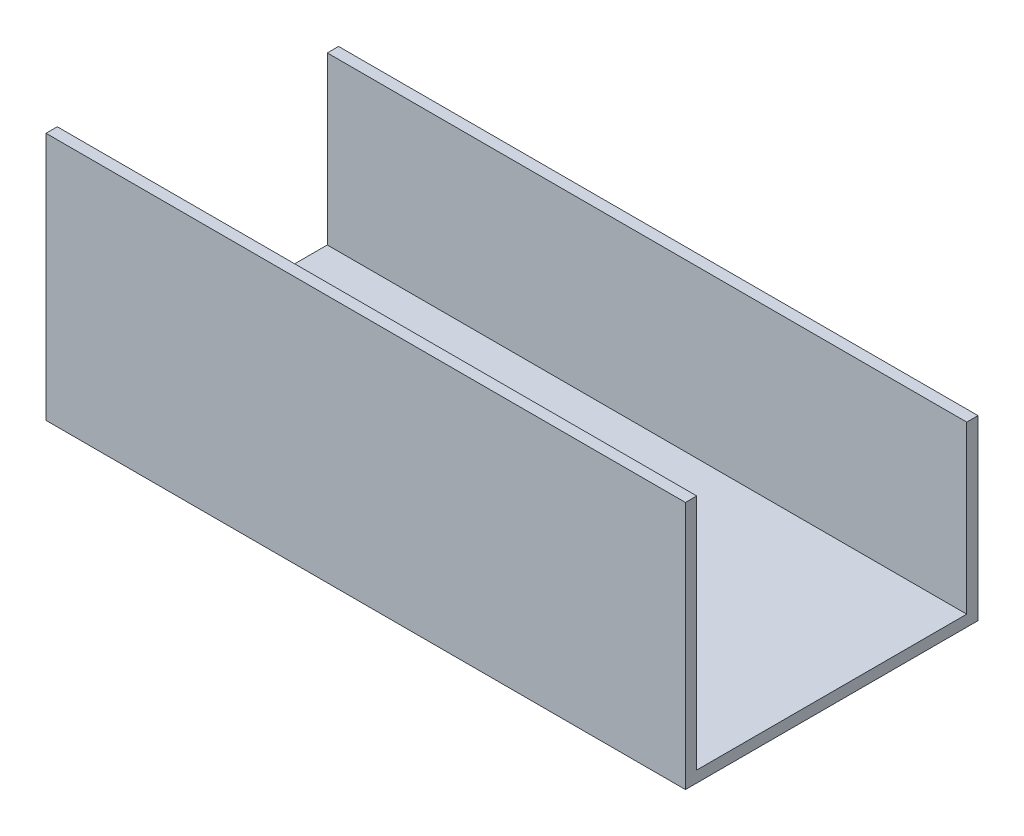
SolidWorks part; units mm, degrees
ref_plane "Front Plane" through (0, 0, 0) normal (0, 0, 1) x (1, 0, 0)
ref_plane "Top Plane" through (0, 0, 0) normal (0, 1, 0) x (1, 0, 0)
ref_plane "Right Plane" through (0, 0, 0) normal (1, 0, 0) x (0, 0, -1)
sketch "Sketch1" plane through (0, 0, 0) normal (1, 0, 0) x (0, 0, -1)
  line L0 (0, 0) -> (0, -66.82)
  line L1 (0, -66.82) -> (76, -66.82)
  line L2 (76, -66.82) -> (76, -20)
  line L3 (76, -20) -> (79.175, -20)
  line L4 (79.175, -20) -> (79.175, -70)
  line L5 (79.175, -70) -> (-3.18, -70)
  line L6 (-3.18, -70) -> (-3.18, 0)
  line L7 (-3.18, 0) -> (0, 0)
  dimension "D1" = 3.175
  dimension "D2" = 3.18
  dimension "D3" = 3.18
  dimension "D4" = 76
  dimension "D5" = 70
  dimension "D6" = 50
extrude "Boss-Extrude1" add sketch "Sketch1" along normal blind 180
